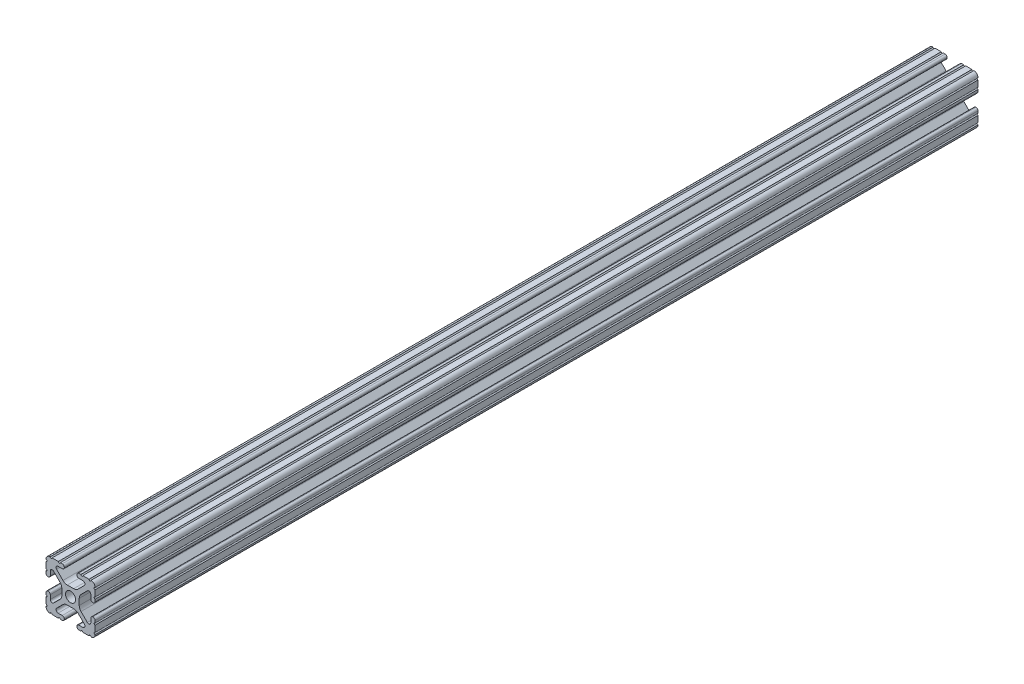
SolidWorks part; units mm, degrees
ref_plane "Front Plane" through (0, 0, 0) normal (0, 0, 1) x (1, 0, 0)
ref_plane "Top Plane" through (0, 0, 0) normal (0, 1, 0) x (1, 0, 0)
ref_plane "Right Plane" through (0, 0, 0) normal (1, 0, 0) x (0, 0, -1)
sketch "Sketch1" plane through (0, 0, 0) normal (0, 0, 1) x (1, 0, 0)
  line L88 (-7.1797, -8.6452) -> (-3.9523, -5.4237)
  line L89 (-1.7093, -4.4958) -> (1.7093, -4.4958)
  line L90 (3.9523, -5.4237) -> (7.1797, -8.6452)
  line L91 (6.4164, -10.4902) -> (4.2875, -10.4902)
  line L92 (3.2385, -11.5392) -> (3.2385, -11.651)
  line L93 (4.2875, -12.7) -> (5.3171, -12.7)
  line L94 (6.3331, -12.7) -> (9.5504, -12.7)
  line L95 (12.7, -9.5504) -> (12.7, -6.3331)
  line L96 (12.7, -5.3171) -> (12.7, -4.2875)
  line L97 (11.651, -3.2385) -> (11.5392, -3.2385)
  line L98 (10.4902, -4.2875) -> (10.4902, -6.4021)
  line L99 (8.7371, -7.1294) -> (5.441, -3.8408)
  line L100 (4.5085, -1.5932) -> (4.5085, 1.5932)
  line L101 (5.441, 3.8408) -> (8.7371, 7.1294)
  line L102 (10.4902, 6.4021) -> (10.4902, 4.2875)
  line L103 (11.5392, 3.2385) -> (11.651, 3.2385)
  line L104 (12.7, 4.2875) -> (12.7, 5.3171)
  line L105 (12.7, 6.3331) -> (12.7, 9.5504)
  line L106 (9.5504, 12.7) -> (6.3331, 12.7)
  line L107 (5.3171, 12.7) -> (4.2875, 12.7)
  line L108 (3.2385, 11.651) -> (3.2385, 11.5392)
  line L109 (4.2875, 10.4902) -> (6.4768, 10.4902)
  line L110 (7.207, 8.7244) -> (3.8983, 5.4232)
  line L111 (1.6558, 4.4958) -> (-1.6558, 4.4958)
  line L112 (-3.8983, 5.4232) -> (-7.207, 8.7244)
  line L113 (-6.4768, 10.4902) -> (-4.2875, 10.4902)
  line L114 (-3.2385, 11.5392) -> (-3.2385, 11.651)
  line L115 (-4.2875, 12.7) -> (-5.3171, 12.7)
  line L116 (-6.3331, 12.7) -> (-9.5504, 12.7)
  line L117 (-12.7, 9.5504) -> (-12.7, 6.3331)
  line L118 (-12.7, 5.3171) -> (-12.7, 4.2875)
  line L119 (-11.651, 3.2385) -> (-11.5392, 3.2385)
  line L120 (-10.4902, 4.2875) -> (-10.4902, 6.4021)
  line L121 (-8.7371, 7.1294) -> (-5.441, 3.8408)
  line L122 (-4.5085, 1.5932) -> (-4.5085, -1.5932)
  line L123 (-5.441, -3.8408) -> (-8.7371, -7.1294)
  line L124 (-10.4902, -6.4021) -> (-10.4902, -4.2875)
  line L125 (-11.5392, -3.2385) -> (-11.651, -3.2385)
  line L126 (-12.7, -4.2875) -> (-12.7, -5.3171)
  line L127 (-12.7, -6.3331) -> (-12.7, -9.5504)
  line L128 (-9.5504, -12.7) -> (-6.3331, -12.7)
  line L129 (-5.3171, -12.7) -> (-4.2875, -12.7)
  line L130 (-3.2385, -11.651) -> (-3.2385, -11.5392)
  line L131 (-4.2875, -10.4902) -> (-6.4164, -10.4902)
  circle A1 centre (0, 0) radius 2.6035
  arc A104 (-7.1797, -8.6452) -> (-6.4164, -10.4902) centre (-6.4164, -9.4098) ccw
  arc A105 (-1.7093, -4.4958) -> (-3.9523, -5.4237) centre (-1.7093, -7.6708) ccw
  arc A106 (3.9523, -5.4237) -> (1.7093, -4.4958) centre (1.7093, -7.6708) ccw
  arc A107 (6.4164, -10.4902) -> (7.1797, -8.6452) centre (6.4164, -9.4098) ccw
  arc A108 (4.2875, -10.4902) -> (3.2385, -11.5392) centre (4.2875, -11.5392) ccw
  arc A109 (3.2385, -11.651) -> (4.2875, -12.7) centre (4.2875, -11.651) ccw
  arc A110 (6.3331, -12.7) -> (5.3171, -12.7) centre (5.8251, -12.7) ccw
  arc A111 (10.5664, -12.6998) -> (9.5504, -12.7) centre (10.0584, -12.7) ccw
  arc A112 (10.5664, -12.6998) -> (12.6998, -10.5664) centre (10.5918, -10.5918) ccw
  arc A113 (12.7, -9.5504) -> (12.6998, -10.5664) centre (12.7, -10.0584) ccw
  arc A114 (12.7, -5.3171) -> (12.7, -6.3331) centre (12.7, -5.8251) ccw
  arc A115 (12.7, -4.2875) -> (11.651, -3.2385) centre (11.651, -4.2875) ccw
  arc A116 (11.5392, -3.2385) -> (10.4902, -4.2875) centre (11.5392, -4.2875) ccw
  arc A117 (8.7371, -7.1294) -> (10.4902, -6.4021) centre (9.4628, -6.4021) ccw
  arc A118 (4.5085, -1.5932) -> (5.441, -3.8408) centre (7.6835, -1.5932) ccw
  arc A119 (5.441, 3.8408) -> (4.5085, 1.5932) centre (7.6835, 1.5932) ccw
  arc A120 (10.4902, 6.4021) -> (8.7371, 7.1294) centre (9.4628, 6.4021) ccw
  arc A121 (10.4902, 4.2875) -> (11.5392, 3.2385) centre (11.5392, 4.2875) ccw
  arc A122 (11.651, 3.2385) -> (12.7, 4.2875) centre (11.651, 4.2875) ccw
  arc A123 (12.7, 6.3331) -> (12.7, 5.3171) centre (12.7, 5.8251) ccw
  arc A124 (12.6998, 10.5664) -> (12.7, 9.5504) centre (12.7, 10.0584) ccw
  arc A125 (12.6998, 10.5664) -> (10.5664, 12.6998) centre (10.5918, 10.5918) ccw
  arc A126 (9.5504, 12.7) -> (10.5664, 12.6998) centre (10.0584, 12.7) ccw
  arc A127 (5.3171, 12.7) -> (6.3331, 12.7) centre (5.8251, 12.7) ccw
  arc A128 (4.2875, 12.7) -> (3.2385, 11.651) centre (4.2875, 11.651) ccw
  arc A129 (3.2385, 11.5392) -> (4.2875, 10.4902) centre (4.2875, 11.5392) ccw
  arc A130 (7.207, 8.7244) -> (6.4768, 10.4902) centre (6.4768, 9.4563) ccw
  arc A131 (1.6558, 4.4958) -> (3.8983, 5.4232) centre (1.6558, 7.6708) ccw
  arc A132 (-3.8983, 5.4232) -> (-1.6558, 4.4958) centre (-1.6558, 7.6708) ccw
  arc A133 (-6.4768, 10.4902) -> (-7.207, 8.7244) centre (-6.4768, 9.4563) ccw
  arc A134 (-4.2875, 10.4902) -> (-3.2385, 11.5392) centre (-4.2875, 11.5392) ccw
  arc A135 (-3.2385, 11.651) -> (-4.2875, 12.7) centre (-4.2875, 11.651) ccw
  arc A136 (-6.3331, 12.7) -> (-5.3171, 12.7) centre (-5.8251, 12.7) ccw
  arc A137 (-10.5664, 12.6998) -> (-9.5504, 12.7) centre (-10.0584, 12.7) ccw
  arc A138 (-10.5664, 12.6998) -> (-12.6998, 10.5664) centre (-10.5918, 10.5918) ccw
  arc A139 (-12.7, 9.5504) -> (-12.6998, 10.5664) centre (-12.7, 10.0584) ccw
  arc A140 (-12.7, 5.3171) -> (-12.7, 6.3331) centre (-12.7, 5.8251) ccw
  arc A141 (-12.7, 4.2875) -> (-11.651, 3.2385) centre (-11.651, 4.2875) ccw
  arc A142 (-11.5392, 3.2385) -> (-10.4902, 4.2875) centre (-11.5392, 4.2875) ccw
  arc A143 (-8.7371, 7.1294) -> (-10.4902, 6.4021) centre (-9.4628, 6.4021) ccw
  arc A144 (-4.5085, 1.5932) -> (-5.441, 3.8408) centre (-7.6835, 1.5932) ccw
  arc A145 (-5.441, -3.8408) -> (-4.5085, -1.5932) centre (-7.6835, -1.5932) ccw
  arc A146 (-10.4902, -6.4021) -> (-8.7371, -7.1294) centre (-9.4628, -6.4021) ccw
  arc A147 (-10.4902, -4.2875) -> (-11.5392, -3.2385) centre (-11.5392, -4.2875) ccw
  arc A148 (-11.651, -3.2385) -> (-12.7, -4.2875) centre (-11.651, -4.2875) ccw
  arc A149 (-12.7, -6.3331) -> (-12.7, -5.3171) centre (-12.7, -5.8251) ccw
  arc A150 (-12.6998, -10.5664) -> (-12.7, -9.5504) centre (-12.7, -10.0584) ccw
  arc A151 (-12.6998, -10.5664) -> (-10.5664, -12.6998) centre (-10.5918, -10.5918) ccw
  arc A152 (-9.5504, -12.7) -> (-10.5664, -12.6998) centre (-10.0584, -12.7) ccw
  arc A153 (-5.3171, -12.7) -> (-6.3331, -12.7) centre (-5.8251, -12.7) ccw
  arc A154 (-4.2875, -12.7) -> (-3.2385, -11.651) centre (-4.2875, -11.651) ccw
  arc A155 (-3.2385, -11.5392) -> (-4.2875, -10.4902) centre (-4.2875, -11.5392) ccw
extrude "Boss-Extrude1" add sketch "Sketch1" along normal mid plane 457.2
